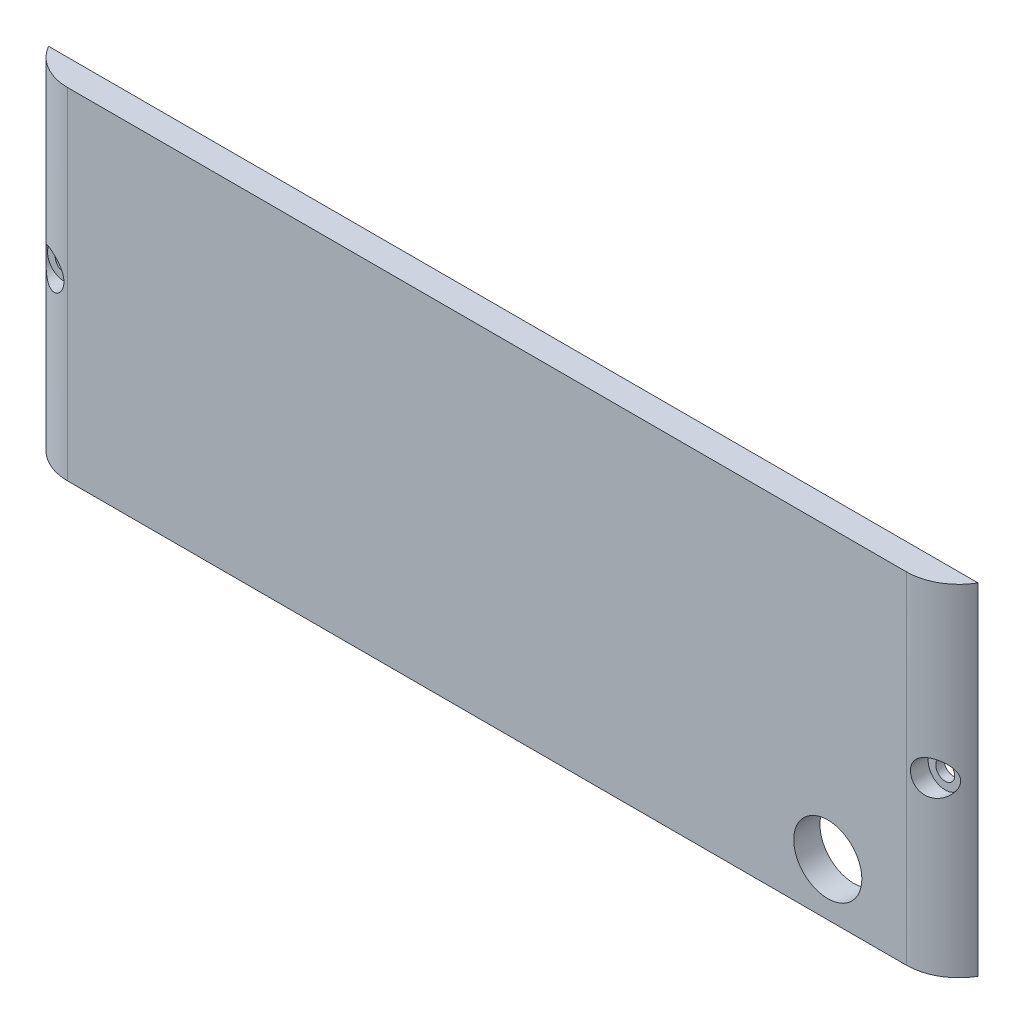
SolidWorks part; units mm, degrees
material "Allzweck-PBT"
ref_plane "Ebene vorne" through (0, 0, 0) normal (0, 0, 1) x (1, 0, 0)
ref_plane "Ebene oben" through (0, 0, 0) normal (0, 1, 0) x (1, 0, 0)
ref_plane "Ebene rechts" through (0, 0, 0) normal (1, 0, 0) x (0, 0, -1)
sketch "Skizze1" plane through (0, 0, 0) normal (0, 0, 1) x (1, 0, 0)
  line L1 (90, 32.5) -> (-90, 32.5)
  line L2 (90, 32.5) -> (90, -32.5)
  line L3 (90, -32.5) -> (-90, -32.5)
  line L4 (-90, 32.5) -> (-90, -32.5)
  line L5 (90, 32.5) -> (-90, -32.5) construction
  line L6 (90, -32.5) -> (-90, 32.5) construction
  point P0 (0, 0)
  dimension "D1" = 180
  dimension "D2" = 65
extrude "Aufsatz-Linear austragen1" add sketch "Skizze1" along normal blind 5
hole_wizard "Stirnsenkung für M3 Zylinderschraube mit Innensechskant1" positions "Skizze4" profile "Skizze5" counterbore size "M3" standard "DIN"
sketch "Skizze4" plane through (0, 0, 5) normal (0, 0, 1) x (1, 0, 0)
  line L0 (-90, 32.5) -> (-90, -32.5) construction
  line L1 (90, -32.5) -> (90, 32.5) construction
  point P0 (-84, 0)
  point P2 (84, 0)
  dimension "D1" = 6
  dimension "6" = 6
sketch "Skizze5" plane through (-84, 0, 5) normal (1, 0, 0) x (0, -1, 0)
  line L0 (0, 0) -> (0, 10.1815)
  line L1 (0, 10.1815) -> (1.8, 9.1)
  line L2 (1.8, 9.1) -> (1.8, 3.4)
  line L3 (1.8, 3.4) -> (3.25, 3.4)
  line L4 (3.25, 3.4) -> (3.25, 0)
  line L5 (3.25, 0) -> (0, 0)
  line L10 (0, 10.1815) -> (-1.8, 9.1) construction
  line L11 (0, -6.35) -> (0, 107.95) construction
  dimension "Bohrerdurchmesser" = 3.6
  dimension "Bohrungstiefe" = 9.1
  dimension "Senkdurchmesser2" = 6.5
  dimension "Senktiefe2" = 3.4
  dimension "Spitzenwinkel" = 118
sketch "Skizze6" plane through (0, 32.5, 0) normal (0, 1, 0) x (1, 0, 0)
  line L0 (-90, -5) -> (-90, 5)
  line L5 (-80, -5) -> (-90, -5)
  line L6 (80, -5) -> (90, -5)
  line L7 (90, -5) -> (90, 5)
  arc A0 (80, -5) -> (90, 5) centre (80, 5) ccw
  arc A1 (-80, -5) -> (-90, 5) centre (-80, 5) cw
  point P9 (-90, -5)
  dimension "D1" = 10
  dimension "D2" = 10
  dimension "D3" = 10
  dimension "D4" = 10
  dimension "D5" = 10
extrude "Schnitt-Linear austragen1" cut sketch "Skizze6" against normal through all
sketch "Skizze7" plane through (0, 0, 5) normal (0, 0, 1) x (1, 0, 0)
  line L0 (-80, -32.5) -> (80, -32.5) construction
  line L4 (80, -32.5) -> (80, 32.5) construction
  circle A0 centre (65, -22.5) radius 6.5
  dimension "D1" = 13
  dimension "D2" = 10
  dimension "D3" = 15
extrude "Schnitt-Linear austragen2" cut sketch "Skizze7" against normal through all
